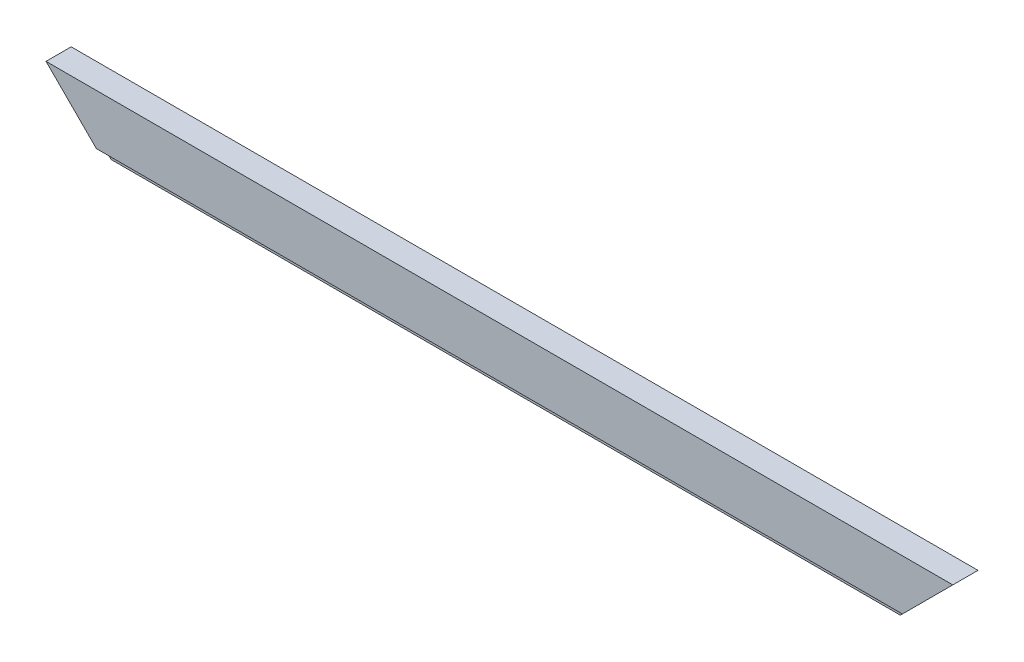
SolidWorks part; units mm, degrees
ref_plane "Front Plane" through (0, 0, 0) normal (0, 0, 1) x (1, 0, 0)
ref_plane "Top Plane" through (0, 0, 0) normal (0, 1, 0) x (1, 0, 0)
ref_plane "Right Plane" through (0, 0, 0) normal (1, 0, 0) x (0, 0, -1)
sketch "Sketch1" plane through (0, 0, 0) normal (0, 0, 1) x (1, 0, 0)
  line L0 (0, 0) -> (1371.6, 0)
  line L1 (0, 0) -> (0, 88.9)
  line L2 (0, 88.9) -> (1371.6, 88.9)
  line L3 (1371.6, 88.9) -> (1371.6, 0)
extrude "Boss-Extrude1" add sketch "Sketch1" along normal blind 38.1
sketch "Sketch2" plane through (0, 0, 38.1) normal (0, 0, 1) x (1, 0, 0)
  line L0 (0, 88.9) -> (88.9, 0)
  line L1 (0, 88.9) -> (0, 0) construction
  line L2 (0, 0) -> (1371.6, 0) construction
  line L3 (0, 88.9) -> (0, 0)
  line L4 (0, 0) -> (88.9, 0)
  dimension "D1" = 88.9
extrude "Cut-Extrude1" cut sketch "Sketch2" against normal up to next
sketch "Sketch3" plane through (0, 0, 38.1) normal (0, 0, 1) x (1, 0, 0)
  line L0 (1371.6, 88.9) -> (1282.7, 0)
  line L1 (88.9, 0) -> (1371.6, 0) construction
  line L2 (1282.7, 0) -> (1371.6, 0)
  line L3 (1371.6, 0) -> (1371.6, 88.9)
  dimension "D1" = 88.9
extrude "Cut-Extrude2" cut sketch "Sketch3" against normal up to next
sketch "Sketch4" plane through (0, 0, 38.1) normal (0, 0, 1) x (1, 0, 0)
  line L3 (88.9, 0) -> (1282.7, 0)
  line L5 (1282.7, 0) -> (1295.4, 12.7)
  line L6 (1371.6, 88.9) -> (1282.7, 0) construction
  line L7 (76.2, 12.7) -> (1295.4, 12.7)
  line L8 (88.9, 0) -> (0, 88.9) construction
  line L9 (88.9, 0) -> (76.2, 12.7)
  dimension "D1" = 12.7
extrude "Cut-Extrude3" cut sketch "Sketch4" against normal blind 9.525
